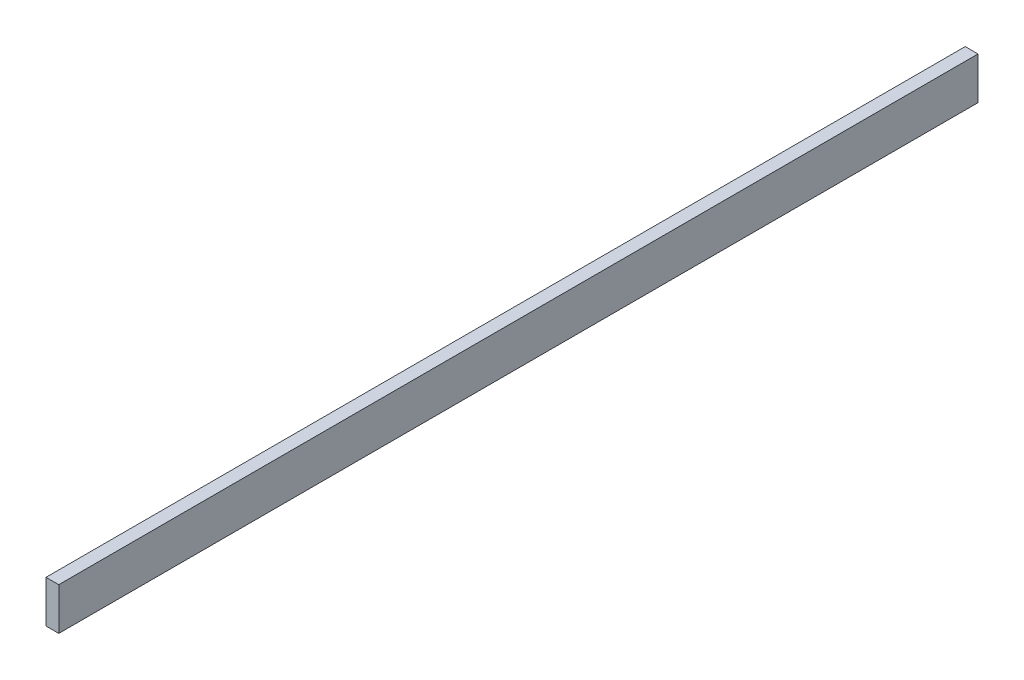
SolidWorks part; units mm, degrees
ref_plane "Front Plane" through (0, 0, 0) normal (0, 0, 1) x (1, 0, 0)
ref_plane "Top Plane" through (0, 0, 0) normal (0, 1, 0) x (1, 0, 0)
ref_plane "Right Plane" through (0, 0, 0) normal (1, 0, 0) x (0, 0, -1)
sketch "Sketch1" plane through (0, 0, 0) normal (0, 0, 1) x (1, 0, 0)
  line L1 (-3.175, -10.5) -> (3.175, -10.5)
  line L2 (-3.175, -10.5) -> (-3.175, 10.5)
  line L3 (-3.175, 10.5) -> (3.175, 10.5)
  line L4 (3.175, -10.5) -> (3.175, 10.5)
  line L5 (-3.175, -10.5) -> (3.175, 10.5) construction
  line L6 (-3.175, 10.5) -> (3.175, -10.5) construction
  point P0 (0, 0)
  dimension "D1" = 6.35
  dimension "D2" = 21
extrude "Boss-Extrude1" add sketch "Sketch1" along normal blind 457.2
